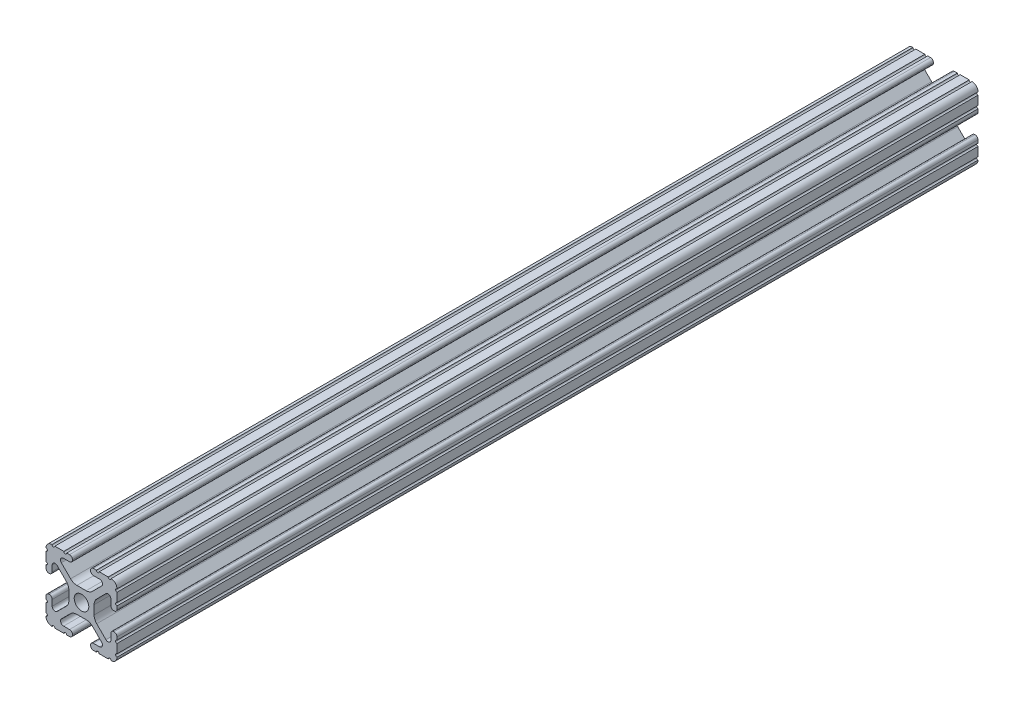
SolidWorks part; units mm, degrees
ref_plane "Front Plane" through (0, 0, 0) normal (0, 0, 1) x (1, 0, 0)
ref_plane "Top Plane" through (0, 0, 0) normal (0, 1, 0) x (1, 0, 0)
ref_plane "Right Plane" through (0, 0, 0) normal (1, 0, 0) x (0, 0, -1)
sketch "Sketch1" plane through (0, 0, 0) normal (0, 0, 1) x (1, 0, 0)
  line L88 (-7.1797, -8.6452) -> (-3.9523, -5.4237)
  line L89 (-1.7093, -4.4958) -> (1.7093, -4.4958)
  line L90 (3.9523, -5.4237) -> (7.1797, -8.6452)
  line L91 (6.4164, -10.4902) -> (4.2875, -10.4902)
  line L92 (3.2385, -11.5392) -> (3.2385, -11.651)
  line L93 (4.2875, -12.7) -> (5.3171, -12.7)
  line L94 (6.3331, -12.7) -> (9.5504, -12.7)
  line L95 (12.7, -9.5504) -> (12.7, -6.3331)
  line L96 (12.7, -5.3171) -> (12.7, -4.2875)
  line L97 (11.651, -3.2385) -> (11.5392, -3.2385)
  line L98 (10.4902, -4.2875) -> (10.4902, -6.4021)
  line L99 (8.7371, -7.1294) -> (5.441, -3.8408)
  line L100 (4.5085, -1.5932) -> (4.5085, 1.5932)
  line L101 (5.441, 3.8408) -> (8.7371, 7.1294)
  line L102 (10.4902, 6.4021) -> (10.4902, 4.2875)
  line L103 (11.5392, 3.2385) -> (11.651, 3.2385)
  line L104 (12.7, 4.2875) -> (12.7, 5.3171)
  line L105 (12.7, 6.3331) -> (12.7, 9.5504)
  line L106 (9.5504, 12.7) -> (6.3331, 12.7)
  line L107 (5.3171, 12.7) -> (4.2875, 12.7)
  line L108 (3.2385, 11.651) -> (3.2385, 11.5392)
  line L109 (4.2875, 10.4902) -> (6.4768, 10.4902)
  line L110 (7.207, 8.7244) -> (3.8983, 5.4232)
  line L111 (1.6558, 4.4958) -> (-1.6558, 4.4958)
  line L112 (-3.8983, 5.4232) -> (-7.207, 8.7244)
  line L113 (-6.4768, 10.4902) -> (-4.2875, 10.4902)
  line L114 (-3.2385, 11.5392) -> (-3.2385, 11.651)
  line L115 (-4.2875, 12.7) -> (-5.3171, 12.7)
  line L116 (-6.3331, 12.7) -> (-9.5504, 12.7)
  line L117 (-12.7, 9.5504) -> (-12.7, 6.3331)
  line L118 (-12.7, 5.3171) -> (-12.7, 4.2875)
  line L119 (-11.651, 3.2385) -> (-11.5392, 3.2385)
  line L120 (-10.4902, 4.2875) -> (-10.4902, 6.4021)
  line L121 (-8.7371, 7.1294) -> (-5.441, 3.8408)
  line L122 (-4.5085, 1.5932) -> (-4.5085, -1.5932)
  line L123 (-5.441, -3.8408) -> (-8.7371, -7.1294)
  line L124 (-10.4902, -6.4021) -> (-10.4902, -4.2875)
  line L125 (-11.5392, -3.2385) -> (-11.651, -3.2385)
  line L126 (-12.7, -4.2875) -> (-12.7, -5.3171)
  line L127 (-12.7, -6.3331) -> (-12.7, -9.5504)
  line L128 (-9.5504, -12.7) -> (-6.3331, -12.7)
  line L129 (-5.3171, -12.7) -> (-4.2875, -12.7)
  line L130 (-3.2385, -11.651) -> (-3.2385, -11.5392)
  line L131 (-4.2875, -10.4902) -> (-6.4164, -10.4902)
  circle A1 centre (0, 0) radius 2.6035
  arc A104 (-7.1797, -8.6452) -> (-6.4164, -10.4902) centre (-6.4164, -9.4098) ccw
  arc A105 (-1.7093, -4.4958) -> (-3.9523, -5.4237) centre (-1.7093, -7.6708) ccw
  arc A106 (3.9523, -5.4237) -> (1.7093, -4.4958) centre (1.7093, -7.6708) ccw
  arc A107 (6.4164, -10.4902) -> (7.1797, -8.6452) centre (6.4164, -9.4098) ccw
  arc A108 (4.2875, -10.4902) -> (3.2385, -11.5392) centre (4.2875, -11.5392) ccw
  arc A109 (3.2385, -11.651) -> (4.2875, -12.7) centre (4.2875, -11.651) ccw
  arc A110 (6.3331, -12.7) -> (5.3171, -12.7) centre (5.8251, -12.7) ccw
  arc A111 (10.5664, -12.6998) -> (9.5504, -12.7) centre (10.0584, -12.7) ccw
  arc A112 (10.5664, -12.6998) -> (12.6998, -10.5664) centre (10.5918, -10.5918) ccw
  arc A113 (12.7, -9.5504) -> (12.6998, -10.5664) centre (12.7, -10.0584) ccw
  arc A114 (12.7, -5.3171) -> (12.7, -6.3331) centre (12.7, -5.8251) ccw
  arc A115 (12.7, -4.2875) -> (11.651, -3.2385) centre (11.651, -4.2875) ccw
  arc A116 (11.5392, -3.2385) -> (10.4902, -4.2875) centre (11.5392, -4.2875) ccw
  arc A117 (8.7371, -7.1294) -> (10.4902, -6.4021) centre (9.4628, -6.4021) ccw
  arc A118 (4.5085, -1.5932) -> (5.441, -3.8408) centre (7.6835, -1.5932) ccw
  arc A119 (5.441, 3.8408) -> (4.5085, 1.5932) centre (7.6835, 1.5932) ccw
  arc A120 (10.4902, 6.4021) -> (8.7371, 7.1294) centre (9.4628, 6.4021) ccw
  arc A121 (10.4902, 4.2875) -> (11.5392, 3.2385) centre (11.5392, 4.2875) ccw
  arc A122 (11.651, 3.2385) -> (12.7, 4.2875) centre (11.651, 4.2875) ccw
  arc A123 (12.7, 6.3331) -> (12.7, 5.3171) centre (12.7, 5.8251) ccw
  arc A124 (12.6998, 10.5664) -> (12.7, 9.5504) centre (12.7, 10.0584) ccw
  arc A125 (12.6998, 10.5664) -> (10.5664, 12.6998) centre (10.5918, 10.5918) ccw
  arc A126 (9.5504, 12.7) -> (10.5664, 12.6998) centre (10.0584, 12.7) ccw
  arc A127 (5.3171, 12.7) -> (6.3331, 12.7) centre (5.8251, 12.7) ccw
  arc A128 (4.2875, 12.7) -> (3.2385, 11.651) centre (4.2875, 11.651) ccw
  arc A129 (3.2385, 11.5392) -> (4.2875, 10.4902) centre (4.2875, 11.5392) ccw
  arc A130 (7.207, 8.7244) -> (6.4768, 10.4902) centre (6.4768, 9.4563) ccw
  arc A131 (1.6558, 4.4958) -> (3.8983, 5.4232) centre (1.6558, 7.6708) ccw
  arc A132 (-3.8983, 5.4232) -> (-1.6558, 4.4958) centre (-1.6558, 7.6708) ccw
  arc A133 (-6.4768, 10.4902) -> (-7.207, 8.7244) centre (-6.4768, 9.4563) ccw
  arc A134 (-4.2875, 10.4902) -> (-3.2385, 11.5392) centre (-4.2875, 11.5392) ccw
  arc A135 (-3.2385, 11.651) -> (-4.2875, 12.7) centre (-4.2875, 11.651) ccw
  arc A136 (-6.3331, 12.7) -> (-5.3171, 12.7) centre (-5.8251, 12.7) ccw
  arc A137 (-10.5664, 12.6998) -> (-9.5504, 12.7) centre (-10.0584, 12.7) ccw
  arc A138 (-10.5664, 12.6998) -> (-12.6998, 10.5664) centre (-10.5918, 10.5918) ccw
  arc A139 (-12.7, 9.5504) -> (-12.6998, 10.5664) centre (-12.7, 10.0584) ccw
  arc A140 (-12.7, 5.3171) -> (-12.7, 6.3331) centre (-12.7, 5.8251) ccw
  arc A141 (-12.7, 4.2875) -> (-11.651, 3.2385) centre (-11.651, 4.2875) ccw
  arc A142 (-11.5392, 3.2385) -> (-10.4902, 4.2875) centre (-11.5392, 4.2875) ccw
  arc A143 (-8.7371, 7.1294) -> (-10.4902, 6.4021) centre (-9.4628, 6.4021) ccw
  arc A144 (-4.5085, 1.5932) -> (-5.441, 3.8408) centre (-7.6835, 1.5932) ccw
  arc A145 (-5.441, -3.8408) -> (-4.5085, -1.5932) centre (-7.6835, -1.5932) ccw
  arc A146 (-10.4902, -6.4021) -> (-8.7371, -7.1294) centre (-9.4628, -6.4021) ccw
  arc A147 (-10.4902, -4.2875) -> (-11.5392, -3.2385) centre (-11.5392, -4.2875) ccw
  arc A148 (-11.651, -3.2385) -> (-12.7, -4.2875) centre (-11.651, -4.2875) ccw
  arc A149 (-12.7, -6.3331) -> (-12.7, -5.3171) centre (-12.7, -5.8251) ccw
  arc A150 (-12.6998, -10.5664) -> (-12.7, -9.5504) centre (-12.7, -10.0584) ccw
  arc A151 (-12.6998, -10.5664) -> (-10.5664, -12.6998) centre (-10.5918, -10.5918) ccw
  arc A152 (-9.5504, -12.7) -> (-10.5664, -12.6998) centre (-10.0584, -12.7) ccw
  arc A153 (-5.3171, -12.7) -> (-6.3331, -12.7) centre (-5.8251, -12.7) ccw
  arc A154 (-4.2875, -12.7) -> (-3.2385, -11.651) centre (-4.2875, -11.651) ccw
  arc A155 (-3.2385, -11.5392) -> (-4.2875, -10.4902) centre (-4.2875, -11.5392) ccw
extrude "Boss-Extrude1" add sketch "Sketch1" along normal mid plane 308
